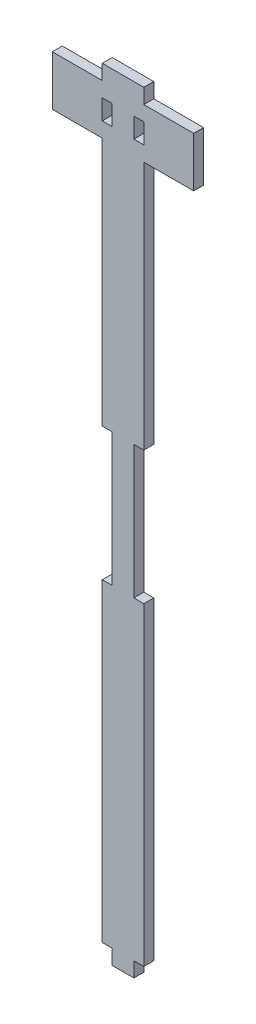
SolidWorks part; units mm, degrees
material "Acrylic (Medium-high impact)"
ref_plane "Front Plane" through (0, 0, 0) normal (0, 0, 1) x (1, 0, 0)
ref_plane "Top Plane" through (0, 0, 0) normal (0, 1, 0) x (1, 0, 0)
ref_plane "Right Plane" through (0, 0, 0) normal (1, 0, 0) x (0, 0, -1)
sketch "Sketch1" plane through (0, 0, 0) normal (0, 0, 1) x (1, 0, 0)
  line L0 (6.3784, 95) -> (6.3784, 20) construction
  line L1 (6.3784, -20) -> (6.3784, -110) construction
  line L2 (-6.1216, -110) -> (-6.1216, -20) construction
  line L3 (-6.1216, 20) -> (-6.1216, 95) construction
  line L4 (6.3784, -110) -> (6.3784, -114.5) construction
  line L5 (6.3784, -114.5) -> (3.3784, -114.5) construction
  line L6 (3.3784, -114.5) -> (3.3784, -119) construction
  line L7 (3.3784, -119) -> (-3.1216, -119) construction
  line L8 (-3.1216, -119) -> (-3.1216, -114.5) construction
  line L9 (-3.1216, -114.5) -> (-6.1216, -114.5) construction
  line L10 (-6.1216, -114.5) -> (-6.1216, -110) construction
  line L11 (-21.1216, 110) -> (-6.1216, 110) construction
  line L12 (6.3784, 110) -> (21.3784, 110) construction
  line L13 (6.3784, 110) -> (6.3784, 114.5) construction
  line L14 (6.3784, 114.5) -> (-6.1216, 114.5) construction
  line L15 (-6.1216, 114.5) -> (-6.1216, 110) construction
  line L16 (6.3784, -114.5) -> (6.3784, -20) construction
  line L17 (6.3784, 110) -> (6.3784, 110.5) construction
  line L18 (6.3784, 20) -> (3.3784, 20) construction
  line L19 (3.3784, 20) -> (3.3784, -20) construction
  line L20 (3.3784, -20) -> (6.3784, -20) construction
  line L21 (-6.1216, 20) -> (-3.1216, 20) construction
  line L22 (-3.1216, 20) -> (-3.1216, -20) construction
  line L23 (-3.1216, -20) -> (-6.1216, -20) construction
  line L24 (21.3784, 110) -> (21.3784, 100) construction
  line L25 (-21.1216, 95) -> (-6.1216, 95) construction
  line L26 (6.3784, 95) -> (21.3784, 95) construction
  line L27 (21.3784, 95) -> (21.3784, 100) construction
  line L28 (-6.1216, 99.5) -> (-6.1216, 105.5) construction
  line L29 (-3.1216, 105.5) -> (-3.1216, 99.5) construction
  line L30 (-6.1216, 105.5) -> (-3.1216, 105.5) construction
  line L31 (-6.1216, 99.5) -> (-3.1216, 99.5) construction
  line L32 (6.3784, 99.5) -> (6.3784, 105.5) construction
  line L33 (3.3784, 105.5) -> (3.3784, 99.5) construction
  line L34 (6.3784, 105.5) -> (3.3784, 105.5) construction
  line L35 (6.3784, 99.5) -> (3.3784, 99.5) construction
  line L36 (-21.1216, 95) -> (-21.1216, 110) construction
sketch "Sketch2" plane through (0, 0, 0) normal (0, 0, 1) x (1, 0, 0)
  line L0 (3.3784, -114.5) -> (3.3784, -119) construction
  line L1 (6.3784, -114.5) -> (3.3784, -114.5) construction
  line L2 (-3.1216, -114.5) -> (-6.1216, -114.5) construction
  line L3 (-3.1216, -119) -> (-3.1216, -114.5) construction
  line L4 (3.3784, -119) -> (-3.1216, -119) construction
  line L5 (-3.1216, -20) -> (-6.1216, -20) construction
  line L6 (3.3784, -20) -> (6.3784, -20) construction
  line L7 (3.3784, 20) -> (3.3784, -20) construction
  line L8 (6.3784, 20) -> (3.3784, 20) construction
  line L9 (-6.1216, 20) -> (-3.1216, 20) construction
  line L10 (-3.1216, 20) -> (-3.1216, -20) construction
  line L11 (6.3784, 95) -> (21.3784, 95) construction
  line L12 (6.3784, 95) -> (6.3784, 20) construction
  line L13 (-6.1216, 20) -> (-6.1216, 95) construction
  line L14 (6.3784, 99.5) -> (6.3784, 105.5) construction
  line L15 (6.3784, 105.5) -> (3.3784, 105.5) construction
  line L16 (3.3784, 105.5) -> (3.3784, 99.5) construction
  line L17 (6.3784, 99.5) -> (3.3784, 99.5) construction
  line L18 (-6.1216, 99.5) -> (-3.1216, 99.5) construction
  line L19 (-3.1216, 105.5) -> (-3.1216, 99.5) construction
  line L20 (-6.1216, 105.5) -> (-3.1216, 105.5) construction
  line L21 (-6.1216, 99.5) -> (-6.1216, 105.5) construction
  line L22 (-21.1216, 95) -> (-6.1216, 95) construction
  line L23 (-21.1216, 95) -> (-21.1216, 110) construction
  line L24 (6.3784, 110) -> (21.3784, 110) construction
  line L25 (6.3784, 110) -> (6.3784, 114.5) construction
  line L26 (-6.1216, 114.5) -> (-6.1216, 110) construction
  line L27 (-21.1216, 110) -> (-6.1216, 110) construction
  line L28 (6.3784, 114.5) -> (-6.1216, 114.5) construction
  line L29 (3.3784, -114.5) -> (3.3784, -119)
  line L30 (6.3784, -114.5) -> (3.3784, -114.5)
  line L31 (-3.1216, -114.5) -> (-6.1216, -114.5)
  line L32 (-3.1216, -119) -> (-3.1216, -114.5)
  line L33 (3.3784, -119) -> (-3.1216, -119)
  line L34 (-3.1216, -20) -> (-6.1216, -20)
  line L35 (3.3784, -20) -> (6.3784, -20)
  line L36 (3.3784, 20) -> (3.3784, -20)
  line L37 (6.3784, 20) -> (3.3784, 20)
  line L38 (-6.1216, 20) -> (-3.1216, 20)
  line L39 (-3.1216, 20) -> (-3.1216, -20)
  line L40 (6.3784, 95) -> (21.3784, 95)
  line L41 (6.3784, 95) -> (6.3784, 20)
  line L42 (-6.1216, 20) -> (-6.1216, 95)
  line L43 (6.3784, 99.5) -> (6.3784, 105.5)
  line L44 (6.3784, 105.5) -> (3.3784, 105.5)
  line L45 (3.3784, 105.5) -> (3.3784, 99.5)
  line L46 (6.3784, 99.5) -> (3.3784, 99.5)
  line L47 (-6.1216, 99.5) -> (-3.1216, 99.5)
  line L48 (-3.1216, 105.5) -> (-3.1216, 99.5)
  line L49 (-6.1216, 105.5) -> (-3.1216, 105.5)
  line L50 (-6.1216, 99.5) -> (-6.1216, 105.5)
  line L51 (-21.1216, 95) -> (-6.1216, 95)
  line L52 (-21.1216, 95) -> (-21.1216, 110)
  line L53 (6.3784, 110) -> (21.3784, 110)
  line L54 (6.3784, 110) -> (6.3784, 114.5)
  line L55 (-6.1216, 114.5) -> (-6.1216, 110)
  line L56 (-21.1216, 110) -> (-6.1216, 110)
  line L57 (6.3784, 114.5) -> (-6.1216, 114.5)
  line L58 (21.3784, 110) -> (21.3784, 95)
  line L59 (6.3784, -20) -> (6.3784, -114.5)
  line L60 (-6.1216, -20) -> (-6.1216, -114.5)
extrude "Boss-Extrude1" add sketch "Sketch2" along normal blind 3
